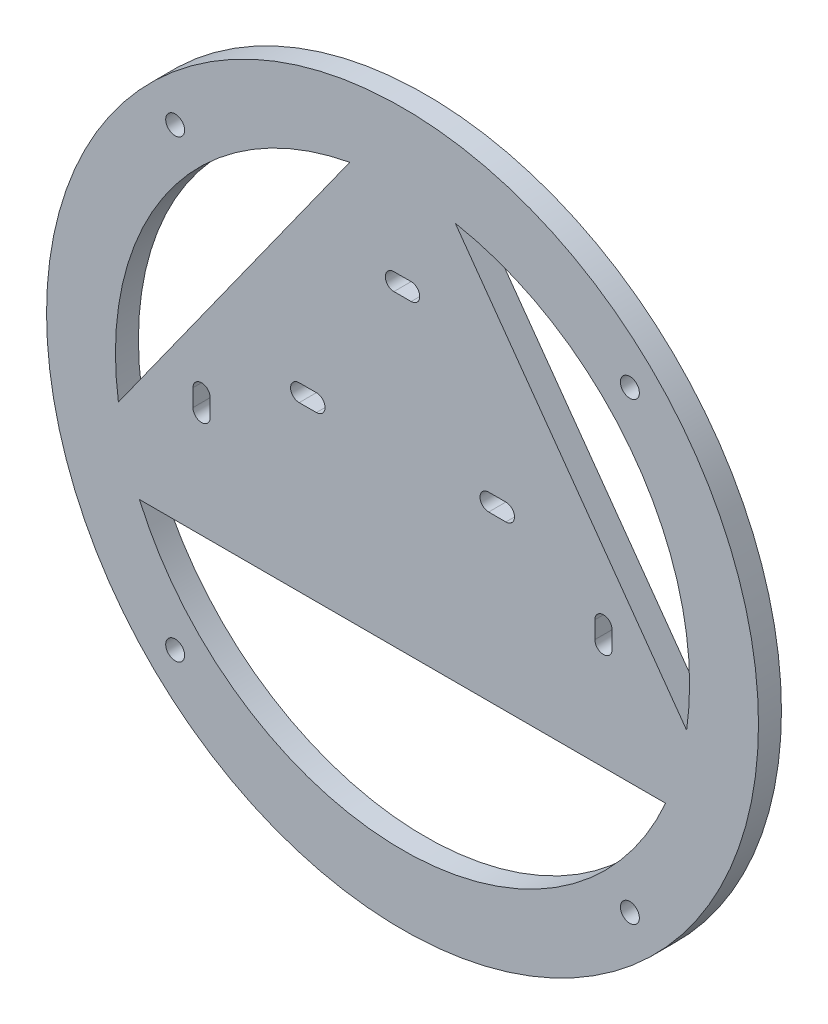
SolidWorks part; units mm, degrees
ref_plane "前视基准面" through (0, 0, 0) normal (0, 0, 1) x (1, 0, 0)
ref_plane "上视基准面" through (0, 0, 0) normal (0, 1, 0) x (1, 0, 0)
ref_plane "右视基准面" through (0, 0, 0) normal (1, 0, 0) x (0, 0, -1)
sketch "草图1" plane through (0, 0, 0) normal (0, 0, 1) x (1, 0, 0)
  line L0 (0, 0) -> (0, 62)
  line L4 (0, 0) -> (-53.6936, -31)
  line L5 (0, 0) -> (53.6936, -31)
  line L6 (-53.6936, -31) -> (-12.251, -7.0731)
  line L7 (0, 62) -> (12, 62)
  line L8 (0, 62) -> (0, 7.4328)
  line L9 (0, 7.4328) -> (12, 7.4328)
  line L10 (12, 62) -> (12, 7.4328)
  line L11 (-53.6936, -31) -> (-59.6936, -20.6077)
  line L12 (-12.251, -7.0731) -> (-18.251, 3.3192)
  line L13 (-59.6936, -20.6077) -> (-18.251, 3.3192)
  line L14 (53.6936, -31) -> (6.3112, -3.6438)
  line L15 (53.6936, -31) -> (47.6936, -41.3923)
  line L16 (6.3112, -3.6438) -> (0.3112, -14.0361)
  line L17 (47.6936, -41.3923) -> (0.3112, -14.0361)
  line L18 (-53.6936, -31) -> (-59.6936, -20.6077)
  line L19 (-53.6936, -31) -> (-103.057, -59.5)
  line L20 (-59.6936, -20.6077) -> (-109.057, -49.1077)
  line L21 (-103.057, -59.5) -> (-109.057, -49.1077)
  line L22 (0, 62) -> (12, 62)
  line L23 (0, 62) -> (0, 119)
  line L24 (12, 62) -> (12, 119)
  line L25 (0, 119) -> (12, 119)
  line L26 (47.6936, -41.3923) -> (53.6936, -31)
  line L27 (47.6936, -41.3923) -> (97.057, -69.8923)
  line L28 (53.6936, -31) -> (103.057, -59.5)
  line L29 (97.057, -69.8923) -> (103.057, -59.5)
  line L30 (-18, 10) -> (-15, 10) construction
  line L33 (0, 15) -> (0, -15) construction
  line L34 (0, 10) -> (10.4368, 10) construction
  line L37 (-1.5, 35) -> (1.5, 35) construction
  line L40 (-1.5, 36.5) -> (1.5, 36.5)
  line L41 (-1.5, 33.5) -> (1.5, 33.5)
  line L42 (-18, 11.5) -> (-15, 11.5)
  line L43 (-18, 8.5) -> (-15, 8.5)
  line L44 (18, 10) -> (15, 10) construction
  line L45 (18, 11.5) -> (15, 11.5)
  line L46 (18, 8.5) -> (15, 8.5)
  line L47 (35, 1.5) -> (35, -1.5) construction
  line L48 (36.5, 1.5) -> (36.5, -1.5)
  line L49 (33.5, 1.5) -> (33.5, -1.5)
  line L53 (-35, -1.5) -> (-35, 1.5) construction
  line L54 (-36.5, -1.5) -> (-36.5, 1.5)
  line L55 (-33.5, -1.5) -> (-33.5, 1.5)
  line L56 (0, 62) -> (-58.6783, -20.0215)
  line L57 (-58.6783, -20.0215) -> (58.6783, -20.0215)
  line L58 (58.6783, -20.0215) -> (0, 62)
  line L62 (1.5, -35) -> (-1.5, -35) construction
  line L63 (1.5, -36.5) -> (-1.5, -36.5)
  line L64 (1.5, -33.5) -> (-1.5, -33.5)
  line L65 (1.5, -35) -> (-1.5, -35) construction
  line L66 (1.5, -36.5) -> (-1.5, -36.5)
  line L67 (1.5, -33.5) -> (-1.5, -33.5)
  circle A0 centre (0, 0) radius 62
  circle A1 centre (0, 0) radius 50
  circle A2 centre (0, 0) radius 100
  arc A10 (-1.5, 36.5) -> (-1.5, 33.5) centre (-1.5, 35) ccw
  arc A11 (1.5, 33.5) -> (1.5, 36.5) centre (1.5, 35) ccw
  circle A12 centre (0, 10) radius 18 construction
  arc A13 (-18, 11.5) -> (-18, 8.5) centre (-18, 10) ccw
  arc A14 (-15, 8.5) -> (-15, 11.5) centre (-15, 10) ccw
  arc A15 (18, 11.5) -> (18, 8.5) centre (18, 10) cw
  arc A16 (15, 8.5) -> (15, 11.5) centre (15, 10) cw
  arc A17 (36.5, 1.5) -> (33.5, 1.5) centre (35, 1.5) ccw
  arc A18 (33.5, -1.5) -> (36.5, -1.5) centre (35, -1.5) ccw
  arc A21 (-36.5, -1.5) -> (-33.5, -1.5) centre (-35, -1.5) ccw
  arc A22 (-33.5, 1.5) -> (-36.5, 1.5) centre (-35, 1.5) ccw
  arc A27 (1.5, -36.5) -> (1.5, -33.5) centre (1.5, -35) ccw
  arc A28 (-1.5, -33.5) -> (-1.5, -36.5) centre (-1.5, -35) ccw
  point P29 (-16.5, 10)
  point P38 (16.5, 10)
  point P43 (0, 35)
  point P55 (35, 0)
  point P69 (-35, 0)
  point P72 (0, 0)
  point P75 (0, 0)
  point P77 (0, -35)
  point P84 (0, -35)
  point P91 (0, -35)
  dimension "D1" = 10
  dimension "D2" = 25
  dimension "D4" = 1.5
  dimension "D5" = 3
  dimension "D6" = 1.5
  dimension "D3" = 3
  dimension "D7" = 4
extrude "凸台-拉伸1" add sketch "草图1" along normal blind 4 contours L4 L57 L17 L16 L5 | L17 L57 L5 L16 | L57 A1 L58 L10 L9 L0 L5 A18 L49 A17 L48 L46 A16 L45 A15 | A10 L40 L8 A1 L56 L13 L12 L4 L0 L41 A22 L55 A21 L54 A14 L43 A13 L42 | A11 L41 L0 L9 L10 L58 A1 L8 L40 | A1 L0 L56 | A1 L58 L0 | L13 A1 L57 L4 L12 | A1 L56 A0 | A1 L56 L13 | A1 L13 L57 | A1 L57 A0 L4 | A1 L4 A0 L17 | A1 L17 A0 L5 | A1 L5 A0 L57 | A1 L57 L58 | A1 L58 A0 L10 | A1 L10 A0 L58 | L20 L21 L19 | L27 L29 L28
hole_wizard "M4 螺纹孔1" positions "草图5" profile "草图6" tap size "M4" standard "GB"
sketch "草图5" plane through (0, 0, 4) normal (0, 0, 1) x (1, 0, 0)
  point P0 (-39.598, 39.598)
  point P6 (-39.598, -39.598)
  point P10 (39.598, -39.598)
  point P14 (39.598, 39.598)
  point P28 (84.4686, -55.6962)
  point P32 (68.8801, -46.6962)
  point P35 (6, 81)
  point P38 (6, 100)
sketch "草图6" plane through (-39.598, 39.598, 4) normal (1, 0, 0) x (0, -1, 0)
  line L0 (0, 0) -> (0, 11.0914)
  line L1 (0, 11.0914) -> (1.65, 10.1)
  line L2 (1.65, 10.1) -> (1.65, 0)
  line L5 (1.65, 0) -> (0, 0)
  line L10 (0, 11.0914) -> (-1.65, 10.1) construction
  line L11 (0, -6.35) -> (0, 107.95) construction
  dimension "螺纹孔钻头直径" = 3.3
  dimension "螺纹孔钻头深度" = 10.1
  dimension "导头角度" = 118
cosmetic thread "孔螺蚊线1" parameters "D1"=8, "D2"=4.3
cosmetic thread "孔螺蚊线2" parameters "D1"=8, "D2"=4.3
cosmetic thread "孔螺蚊线3" parameters "D1"=8, "D2"=4.3
cosmetic thread "孔螺蚊线4" parameters "D1"=8, "D2"=4.3
